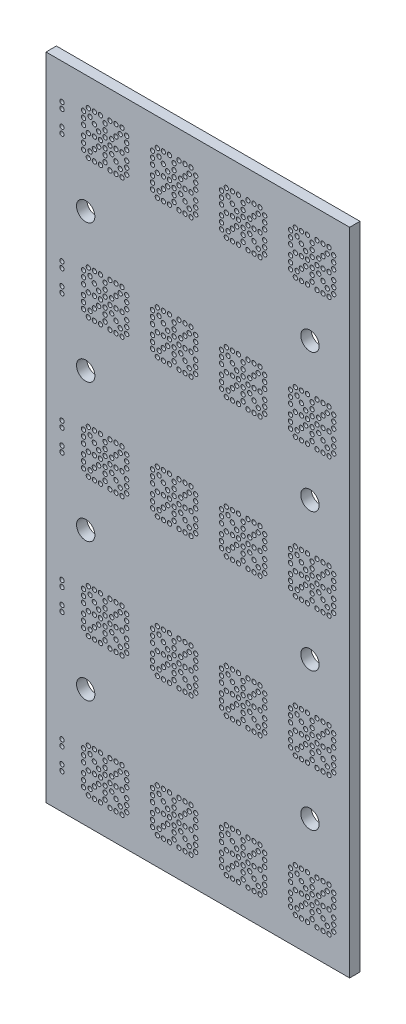
SolidWorks part; units mm, degrees
material "ABS PC"
ref_plane "Front Plane" through (0, 0, 0) normal (0, 0, 1) x (1, 0, 0)
ref_plane "Top Plane" through (0, 0, 0) normal (0, 1, 0) x (1, 0, 0)
ref_plane "Right Plane" through (0, 0, 0) normal (1, 0, 0) x (0, 0, -1)
sketch "Sketch1" plane through (0, 0, 0) normal (0, 0, 1) x (1, 0, 0)
  line L0 (265.9975, 197.0179) -> (342.1693, 194.9479) construction
  line L1 (297.418, 228.3826) -> (298.307, 228.3826) construction
  line L2 (297.418, 228.3826) -> (300.593, 228.3826) construction
  line L3 (302.371, 228.3826) -> (302.371, 231.5576) construction
  line L4 (296.7097, 229.0811) -> (296.7097, 229.9701) construction
  line L5 (296.7097, 230.8591) -> (296.7097, 234.0341) construction
  line L6 (296.7097, 234.0341) -> (299.8847, 234.0341) construction
  line L7 (296.7097, 234.0341) -> (297.0639, 234.3834) construction
  line L8 (296.7097, 234.0341) -> (297.418, 234.7326) construction
  line L9 (299.196, 231.5576) -> (300.593, 231.5576) construction
  line L10 (297.0639, 234.3834) -> (299.5404, 231.9069) construction
  line L11 (296.7097, 232.2561) -> (296.7097, 230.8591)
  line L12 (297.418, 231.5576) -> (296.7097, 231.5576) construction
  line L13 (299.8847, 232.2561) -> (299.196, 231.5576) construction
  line L14 (299.8945, 231.5576) -> (298.9307, 232.5165) construction
  line L15 (299.8945, 231.5576) -> (300.8534, 232.5214) construction
  line L16 (297.418, 234.7326) -> (307.578, 234.7326) construction
  line L17 (293.5347, 230.4146) -> (293.5347, 229.5256) construction
  line L18 (293.5347, 232.7006) -> (293.5347, 230.4146) construction
  line L19 (335.8892, 225.6039) -> (291.1852, 225.6039)
  line L20 (335.8892, 225.6039) -> (335.8892, 237.5114)
  line L21 (335.8892, 237.5114) -> (291.1852, 237.5114)
  line L22 (291.1852, 225.6039) -> (291.1852, 237.5114)
  line L23 (335.8892, 225.6039) -> (291.1852, 237.5114) construction
  line L24 (335.8892, 237.5114) -> (291.1852, 225.6039) construction
  line L25 (333.5397, 232.2561) -> (333.5397, 230.8591) construction
  line L26 (293.5347, 231.5576) -> (333.5397, 231.5576) construction
  circle A0 centre (297.418, 228.3826) radius 0.3175
  circle A3 centre (298.307, 228.3826) radius 0.3175
  circle A4 centre (299.196, 228.3826) radius 0.3175
  circle A5 centre (300.593, 228.3826) radius 0.3175
  circle A6 centre (301.482, 228.3826) radius 0.3175
  circle A7 centre (302.371, 228.3826) radius 0.3175
  circle A8 centre (302.371, 231.5576) radius 0.3175
  circle A9 centre (301.482, 231.5576) radius 0.3175
  circle A10 centre (300.593, 231.5576) radius 0.3175
  circle A11 centre (299.196, 231.5576) radius 0.3175
  circle A12 centre (298.307, 231.5576) radius 0.3175
  circle A13 centre (297.418, 231.5576) radius 0.3175
  circle A14 centre (302.371, 234.7326) radius 0.3175
  circle A15 centre (301.482, 234.7326) radius 0.3175
  circle A16 centre (300.593, 234.7326) radius 0.3175
  circle A17 centre (299.196, 234.7326) radius 0.3175
  circle A18 centre (298.307, 234.7326) radius 0.3175
  circle A19 centre (297.418, 234.7326) radius 0.3175
  circle A20 centre (296.7097, 229.0811) radius 0.3175
  circle A21 centre (296.7097, 229.9701) radius 0.3175
  circle A22 centre (296.7097, 230.8591) radius 0.3175
  circle A23 centre (296.7097, 234.0341) radius 0.3175
  circle A24 centre (296.7097, 233.1451) radius 0.3175
  circle A25 centre (296.7097, 232.2561) radius 0.3175
  circle A26 centre (299.8847, 234.0341) radius 0.3175
  circle A27 centre (299.8847, 233.1451) radius 0.3175
  circle A28 centre (299.8847, 232.2561) radius 0.3175
  circle A29 centre (299.8847, 230.8591) radius 0.3175
  circle A30 centre (299.8847, 229.9701) radius 0.3175
  circle A31 centre (299.8847, 229.0811) radius 0.3175
  circle A32 centre (297.6735, 233.7737) radius 0.3175
  circle A33 centre (298.3021, 233.1451) radius 0.3175
  circle A34 centre (298.9307, 232.5165) radius 0.3175
  circle A35 centre (303.0597, 234.0341) radius 0.3175
  circle A36 centre (303.0597, 233.1451) radius 0.3175
  circle A37 centre (303.0597, 232.2561) radius 0.3175
  circle A38 centre (303.0597, 230.8591) radius 0.3175
  circle A39 centre (303.0597, 229.9701) radius 0.3175
  circle A40 centre (303.0597, 229.0811) radius 0.3175
  circle A41 centre (300.8534, 232.5214) radius 0.3175
  circle A42 centre (301.482, 233.15) radius 0.3175
  circle A43 centre (302.1106, 233.7786) radius 0.3175
  circle A44 centre (300.8582, 230.5987) radius 0.3175
  circle A45 centre (301.4869, 229.9701) radius 0.3175
  circle A46 centre (302.1155, 229.3415) radius 0.3175
  circle A47 centre (298.9356, 230.5939) radius 0.3175
  circle A48 centre (298.307, 229.9653) radius 0.3175
  circle A49 centre (297.6784, 229.3366) radius 0.3175
  circle A50 centre (307.578, 234.7326) radius 0.3175
  circle A51 centre (306.8697, 234.0341) radius 0.3175
  circle A52 centre (306.8697, 233.1451) radius 0.3175
  circle A53 centre (306.8697, 232.2561) radius 0.3175
  circle A54 centre (308.467, 234.7326) radius 0.3175
  circle A55 centre (309.356, 234.7326) radius 0.3175
  circle A56 centre (310.753, 234.7326) radius 0.3175
  circle A57 centre (311.642, 234.7326) radius 0.3175
  circle A58 centre (312.531, 234.7326) radius 0.3175
  circle A59 centre (313.2197, 234.0341) radius 0.3175
  circle A60 centre (313.2197, 233.1451) radius 0.3175
  circle A61 centre (313.2197, 232.2561) radius 0.3175
  circle A62 centre (313.2197, 230.8591) radius 0.3175
  circle A63 centre (313.2197, 229.9701) radius 0.3175
  circle A64 centre (313.2197, 229.0811) radius 0.3175
  circle A65 centre (312.531, 228.3826) radius 0.3175
  circle A66 centre (311.642, 228.3826) radius 0.3175
  circle A67 centre (310.753, 228.3826) radius 0.3175
  circle A68 centre (309.356, 228.3826) radius 0.3175
  circle A69 centre (308.467, 228.3826) radius 0.3175
  circle A70 centre (307.578, 228.3826) radius 0.3175
  circle A71 centre (306.8697, 229.0811) radius 0.3175
  circle A72 centre (306.8697, 229.9701) radius 0.3175
  circle A73 centre (306.8697, 230.8591) radius 0.3175
  circle A74 centre (307.578, 231.5576) radius 0.3175
  circle A75 centre (308.467, 231.5576) radius 0.3175
  circle A76 centre (309.356, 231.5576) radius 0.3175
  circle A77 centre (310.753, 231.5576) radius 0.3175
  circle A78 centre (311.642, 231.5576) radius 0.3175
  circle A79 centre (312.531, 231.5576) radius 0.3175
  circle A80 centre (312.2706, 233.7786) radius 0.3175
  circle A81 centre (311.642, 233.15) radius 0.3175
  circle A82 centre (311.0134, 232.5214) radius 0.3175
  circle A83 centre (310.0447, 232.2561) radius 0.3175
  circle A84 centre (310.0447, 233.1451) radius 0.3175
  circle A85 centre (310.0447, 234.0341) radius 0.3175
  circle A86 centre (309.0907, 232.5165) radius 0.3175
  circle A87 centre (308.4621, 233.1451) radius 0.3175
  circle A88 centre (307.8335, 233.7737) radius 0.3175
  circle A89 centre (307.8384, 229.3366) radius 0.3175
  circle A90 centre (308.467, 229.9653) radius 0.3175
  circle A91 centre (309.0956, 230.5939) radius 0.3175
  circle A92 centre (310.0447, 230.8591) radius 0.3175
  circle A93 centre (310.0447, 229.9701) radius 0.3175
  circle A94 centre (310.0447, 229.0811) radius 0.3175
  circle A95 centre (312.2755, 229.3415) radius 0.3175
  circle A96 centre (311.6469, 229.9701) radius 0.3175
  circle A97 centre (311.0182, 230.5987) radius 0.3175
  circle A98 centre (317.738, 234.7326) radius 0.3175
  circle A99 centre (317.0297, 234.0341) radius 0.3175
  circle A100 centre (317.0297, 233.1451) radius 0.3175
  circle A101 centre (317.0297, 232.2561) radius 0.3175
  circle A102 centre (318.627, 234.7326) radius 0.3175
  circle A103 centre (319.516, 234.7326) radius 0.3175
  circle A104 centre (320.913, 234.7326) radius 0.3175
  circle A105 centre (321.802, 234.7326) radius 0.3175
  circle A106 centre (322.691, 234.7326) radius 0.3175
  circle A107 centre (323.3797, 234.0341) radius 0.3175
  circle A108 centre (323.3797, 233.1451) radius 0.3175
  circle A109 centre (323.3797, 232.2561) radius 0.3175
  circle A110 centre (323.3797, 230.8591) radius 0.3175
  circle A111 centre (323.3797, 229.9701) radius 0.3175
  circle A112 centre (323.3797, 229.0811) radius 0.3175
  circle A113 centre (322.691, 228.3826) radius 0.3175
  circle A114 centre (321.802, 228.3826) radius 0.3175
  circle A115 centre (320.913, 228.3826) radius 0.3175
  circle A116 centre (319.516, 228.3826) radius 0.3175
  circle A117 centre (318.627, 228.3826) radius 0.3175
  circle A118 centre (317.738, 228.3826) radius 0.3175
  circle A119 centre (317.0297, 229.0811) radius 0.3175
  circle A120 centre (317.0297, 229.9701) radius 0.3175
  circle A121 centre (317.0297, 230.8591) radius 0.3175
  circle A122 centre (317.738, 231.5576) radius 0.3175
  circle A123 centre (318.627, 231.5576) radius 0.3175
  circle A124 centre (319.516, 231.5576) radius 0.3175
  circle A125 centre (320.913, 231.5576) radius 0.3175
  circle A126 centre (321.802, 231.5576) radius 0.3175
  circle A127 centre (322.691, 231.5576) radius 0.3175
  circle A128 centre (322.4306, 233.7786) radius 0.3175
  circle A129 centre (321.802, 233.15) radius 0.3175
  circle A130 centre (321.1734, 232.5214) radius 0.3175
  circle A131 centre (320.2047, 232.2561) radius 0.3175
  circle A132 centre (320.2047, 233.1451) radius 0.3175
  circle A133 centre (320.2047, 234.0341) radius 0.3175
  circle A134 centre (319.2507, 232.5165) radius 0.3175
  circle A135 centre (318.6221, 233.1451) radius 0.3175
  circle A136 centre (317.9935, 233.7737) radius 0.3175
  circle A137 centre (317.9984, 229.3366) radius 0.3175
  circle A138 centre (318.627, 229.9653) radius 0.3175
  circle A139 centre (319.2556, 230.5939) radius 0.3175
  circle A140 centre (320.2047, 230.8591) radius 0.3175
  circle A141 centre (320.2047, 229.9701) radius 0.3175
  circle A142 centre (320.2047, 229.0811) radius 0.3175
  circle A143 centre (322.4355, 229.3415) radius 0.3175
  circle A144 centre (321.8069, 229.9701) radius 0.3175
  circle A145 centre (321.1782, 230.5987) radius 0.3175
  circle A146 centre (327.898, 234.7326) radius 0.3175
  circle A147 centre (327.1897, 234.0341) radius 0.3175
  circle A148 centre (327.1897, 233.1451) radius 0.3175
  circle A149 centre (327.1897, 232.2561) radius 0.3175
  circle A150 centre (328.787, 234.7326) radius 0.3175
  circle A151 centre (329.676, 234.7326) radius 0.3175
  circle A152 centre (331.073, 234.7326) radius 0.3175
  circle A153 centre (331.962, 234.7326) radius 0.3175
  circle A154 centre (332.851, 234.7326) radius 0.3175
  circle A155 centre (333.5397, 234.0341) radius 0.3175
  circle A156 centre (333.5397, 233.1451) radius 0.3175
  circle A157 centre (333.5397, 232.2561) radius 0.3175
  circle A158 centre (333.5397, 230.8591) radius 0.3175
  circle A159 centre (333.5397, 229.9701) radius 0.3175
  circle A160 centre (333.5397, 229.0811) radius 0.3175
  circle A161 centre (332.851, 228.3826) radius 0.3175
  circle A162 centre (331.962, 228.3826) radius 0.3175
  circle A163 centre (331.073, 228.3826) radius 0.3175
  circle A164 centre (329.676, 228.3826) radius 0.3175
  circle A165 centre (328.787, 228.3826) radius 0.3175
  circle A166 centre (327.898, 228.3826) radius 0.3175
  circle A167 centre (327.1897, 229.0811) radius 0.3175
  circle A168 centre (327.1897, 229.9701) radius 0.3175
  circle A169 centre (327.1897, 230.8591) radius 0.3175
  circle A170 centre (327.898, 231.5576) radius 0.3175
  circle A171 centre (328.787, 231.5576) radius 0.3175
  circle A172 centre (329.676, 231.5576) radius 0.3175
  circle A173 centre (331.073, 231.5576) radius 0.3175
  circle A174 centre (331.962, 231.5576) radius 0.3175
  circle A175 centre (332.851, 231.5576) radius 0.3175
  circle A176 centre (332.5906, 233.7786) radius 0.3175
  circle A177 centre (331.962, 233.15) radius 0.3175
  circle A178 centre (331.3334, 232.5214) radius 0.3175
  circle A179 centre (330.3647, 232.2561) radius 0.3175
  circle A180 centre (330.3647, 233.1451) radius 0.3175
  circle A181 centre (330.3647, 234.0341) radius 0.3175
  circle A182 centre (329.4107, 232.5165) radius 0.3175
  circle A183 centre (328.7821, 233.1451) radius 0.3175
  circle A184 centre (328.1535, 233.7737) radius 0.3175
  circle A185 centre (328.1584, 229.3366) radius 0.3175
  circle A186 centre (328.787, 229.9653) radius 0.3175
  circle A187 centre (329.4156, 230.5939) radius 0.3175
  circle A188 centre (330.3647, 230.8591) radius 0.3175
  circle A189 centre (330.3647, 229.9701) radius 0.3175
  circle A190 centre (330.3647, 229.0811) radius 0.3175
  circle A191 centre (332.5955, 229.3415) radius 0.3175
  circle A192 centre (331.9669, 229.9701) radius 0.3175
  circle A193 centre (331.3382, 230.5987) radius 0.3175
  circle A194 centre (293.5347, 229.5256) radius 0.3175
  circle A195 centre (293.5347, 230.4146) radius 0.3175
  circle A196 centre (293.5347, 233.5896) radius 0.3175
  circle A197 centre (293.5347, 232.7006) radius 0.3175
  point P81 (299.8945, 231.5576)
  point P96 (298.3021, 233.1451)
  point P410 (293.5347, 229.9701)
  point P411 (313.5372, 231.5576)
  point P422 (313.5372, 231.5576)
  dimension "D2" = 0.635
  dimension "D1" = 76.2
  dimension "D4" = 0.889
  dimension "D6" = 3.175
  dimension "D8" = 3.175
  dimension "D10" = 0.889
  dimension "D12" = 3.175
  dimension "D14" = 3.175
  dimension "D15" = 0.7082
  dimension "D16" = 0.889
  dimension "D17" = 0.889
  dimension "D19" = 90
  dimension "D20" = 1.3595
  dimension "D22" = 10.16
  dimension "D23" = 0.889
  dimension "D24" = 3.175
  dimension "D25" = 11.9075
  dimension "D26" = 44.704
  dimension "D3" = 3
  dimension "D5" = 2
  dimension "D7" = 3
  dimension "D9" = 3
  dimension "D11" = 2
  dimension "D13" = 3
  dimension "D21" = 4
  dimension "D18" = 4
extrude "Boss-Extrude1" add sketch "Sketch1" along normal blind 1.524 contours L22 L19 L20 L21 A196 A195 A194 A193 A192 A191 A190 A189 A188 A187 A186 A185 A184 A183 A182 A181 A180 A179 A178 A177 A176 A175 A174
pattern_linear "LPattern1" count 5 spacing 20.32 along (0, -1, 0) of "Boss-Extrude1"
sketch "Sketch2" plane through (0, 0, 1.524) normal (0, 0, 1) x (1, 0, 0)
  line L1 (291.1852, 217.1914) -> (335.8892, 217.1914)
  line L2 (291.1852, 217.1914) -> (291.1852, 225.6039)
  line L3 (291.1852, 225.6039) -> (335.8892, 225.6039)
  line L4 (335.8892, 217.1914) -> (335.8892, 225.6039)
  line L5 (291.1852, 196.8714) -> (335.8892, 196.8714)
  line L6 (291.1852, 196.8714) -> (291.1852, 205.2839)
  line L7 (291.1852, 205.2839) -> (335.8892, 205.2839)
  line L8 (335.8892, 196.8714) -> (335.8892, 205.2839)
  line L9 (291.1852, 176.5514) -> (335.8892, 176.5514)
  line L10 (291.1852, 176.5514) -> (291.1852, 184.9639)
  line L11 (291.1852, 184.9639) -> (335.8892, 184.9639)
  line L12 (335.8892, 176.5514) -> (335.8892, 184.9639)
  line L13 (291.1852, 156.2314) -> (335.8892, 156.2314)
  line L14 (291.1852, 156.2314) -> (291.1852, 164.6439)
  line L15 (291.1852, 164.6439) -> (335.8892, 164.6439)
  line L16 (335.8892, 156.2314) -> (335.8892, 164.6439)
  line L17 (291.1852, 237.5114) -> (335.8892, 237.5114)
  line L18 (291.1852, 237.5114) -> (291.1852, 238.7814)
  line L19 (291.1852, 238.7814) -> (335.8892, 238.7814)
  line L20 (335.8892, 237.5114) -> (335.8892, 238.7814)
  line L21 (291.1852, 144.3239) -> (335.8892, 144.3239)
  line L22 (291.1852, 144.3239) -> (291.1852, 143.0539)
  line L23 (291.1852, 143.0539) -> (335.8892, 143.0539)
  line L24 (335.8892, 144.3239) -> (335.8892, 143.0539)
  dimension "D1" = 1.27
extrude "Boss-Extrude2" add sketch "Sketch2" against normal up to surface (1.524 mm away) up to face at (297.0272, 230.8591, 0)
hole_wizard "#2 Clearance Hole1" positions "Sketch3" profile "Sketch4" hole size "#2" standard "ANSI Inch"
sketch "Sketch3" plane through (0, 0, 1.524) normal (0, 0, 1) x (1, 0, 0)
  point P0 (297.0272, 221.3983)
  point P3 (330.0472, 221.3983)
  point P6 (330.0472, 201.0783)
  point P9 (297.0272, 201.0783)
  point P12 (297.0272, 180.7583)
  point P15 (330.0472, 180.7583)
  point P18 (330.0472, 160.4383)
  point P21 (297.0272, 160.4383)
sketch "Sketch4" plane through (297.0272, 221.3983, 1.524) normal (1, 0, 0) x (0, -1, 0)
  line L0 (0, 0) -> (0, 1.524)
  line L1 (0, 1.524) -> (1.3525, 1.524)
  line L2 (1.3525, 1.524) -> (1.3525, 0)
  line L5 (1.3525, 0) -> (0, 0)
  line L11 (0, -6.35) -> (0, 107.95) construction
  dimension "Thru Hole Dia." = 2.7051
  dimension "Thru Hole Depth" = 1.524
